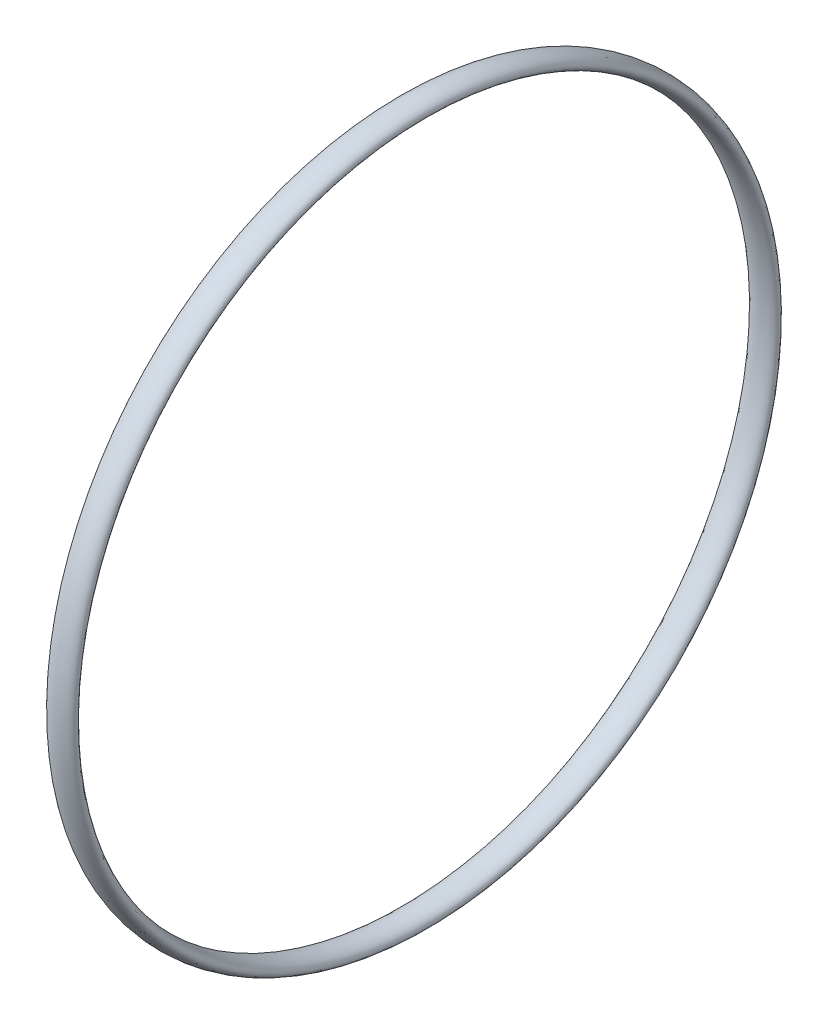
SolidWorks part; units mm, degrees
ref_plane "Front Plane" through (0, 0, 0) normal (0, 0, 1) x (1, 0, 0)
ref_plane "Top Plane" through (0, 0, 0) normal (0, 1, 0) x (1, 0, 0)
ref_plane "Right Plane" through (0, 0, 0) normal (1, 0, 0) x (0, 0, -1)
ref_plane "Plane5" through (0, 0, -15.7927) normal (0, 0, -1) x (-1, 0, 0)
sketch "Sketch3" plane through (3.2076, 0.8846, -15.7927) normal (0, 0, -1) x (-0.8586, -0.5126, 0)
  line L0 (8.4073, 6.511) -> (-4.2125, -1.0223) construction
  line L1 (-7.3732, 18.6096) -> (11.568, -13.1209) construction
  line L2 (-7.3732, 18.6096) -> (11.568, -13.1209) construction
  circle A0 centre (-7.3732, 18.6096) radius 0.75 construction
  ellipse E0 centre (-7.3732, 18.6096) end of major axis (-6.7292, 18.994) minor radius 0.375
  point P3 (-6.9888, 17.9656)
  point P5 (2.0974, 2.7443)
  point P11 (-7.3732, 18.6096)
  point P28 (11.568, -13.1209)
  dimension "D2" = 1.5
  dimension "D1" = 0.75
revolve "Revolve1" add sketch "Sketch3" angle 360 about L0
equation "\"straplength\"= \"D2@Sketch1\""
equation "\"D1@Sketch1\"= \"straplength\" / 3.1416"
